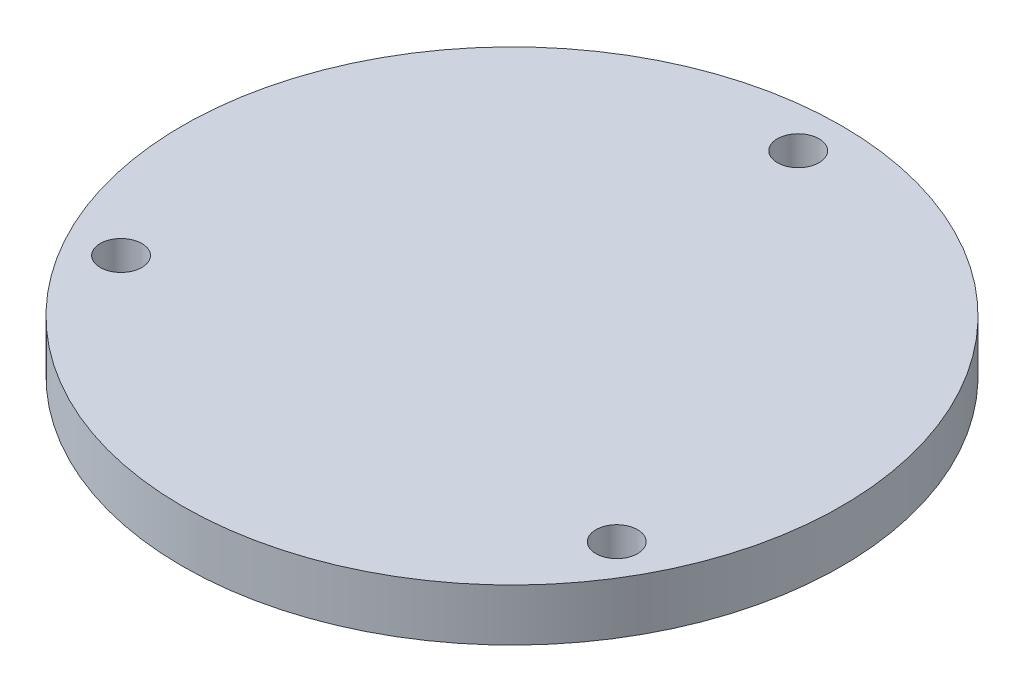
SolidWorks part; units mm, degrees
ref_plane "정면" through (0, 0, 0) normal (0, 0, 1) x (1, 0, 0)
ref_plane "윗면" through (0, 0, 0) normal (0, 1, 0) x (1, 0, 0)
ref_plane "우측면" through (0, 0, 0) normal (1, 0, 0) x (0, 0, -1)
sketch "스케치1" plane through (0, 0, 0) normal (0, 1, 0) x (1, 0, 0)
  circle A0 centre (0, 0) radius 19
  dimension "D1" = 38
extrude "보스-돌출1" add sketch "스케치1" along normal blind 3
hole_wizard "M2 여유 구멍1" positions "스케치2" profile "스케치3" hole size "M2" standard "ISO" end condition through all
sketch "스케치2" plane through (0, 3, 0) normal (0, 1, 0) x (1, 0, 0)
  line L1 (0, 16.5) -> (-14.2894, -8.25)
  line L2 (-14.2894, -8.25) -> (14.2894, -8.25)
  line L3 (14.2894, -8.25) -> (0, 16.5)
  circle A0 centre (0, 0) radius 16.5 construction
  point P3 (0, 16.5)
  point P4 (-14.2894, -8.25)
  point P5 (14.2894, -8.25)
  point P17 (0, 0)
  dimension "D1" = 33
sketch "스케치3" plane through (14.2894, 3, 8.25) normal (1, 0, 0) x (0, 0, 1)
  line L0 (0, 0) -> (0, 3)
  line L1 (0, 3) -> (1.2, 3)
  line L2 (1.2, 3) -> (1.2, 0)
  line L5 (1.2, 0) -> (0, 0)
  line L11 (0, -6.35) -> (0, 107.95) construction
  dimension "관통 구멍 지름" = 2.4
  dimension "관통 구멍 깊이" = 3
